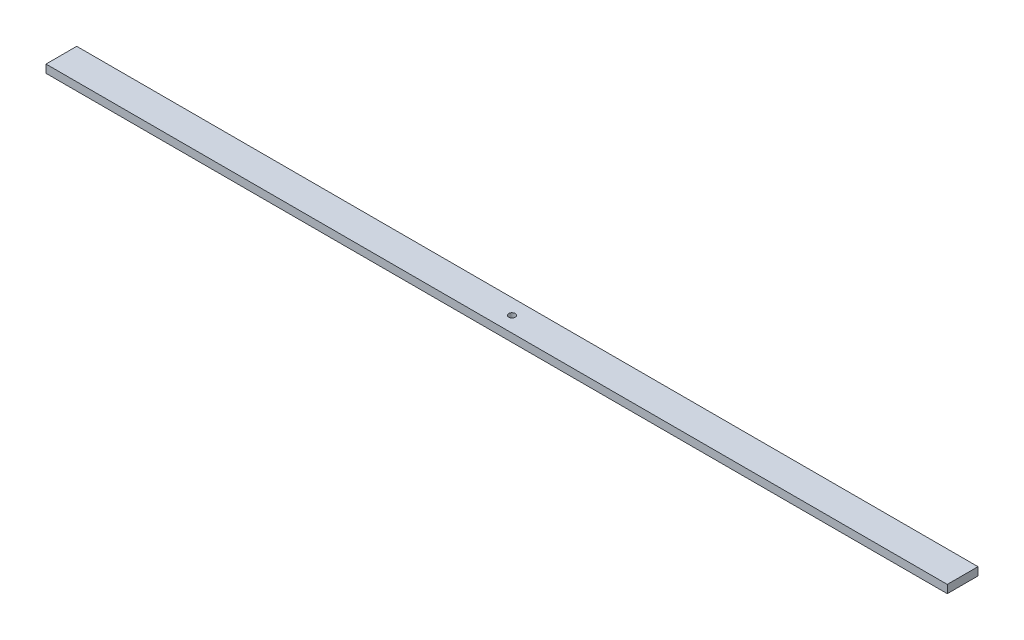
SolidWorks part; units mm, degrees
material "Thornel Mat VMA"
ref_plane "Front Plane" through (0, 0, 0) normal (0, 0, 1) x (1, 0, 0)
ref_plane "Top Plane" through (0, 0, 0) normal (0, 1, 0) x (1, 0, 0)
ref_plane "Right Plane" through (0, 0, 0) normal (1, 0, 0) x (0, 0, -1)
sketch "Sketch1" plane through (0, 0, 0) normal (0, 1, 0) x (1, 0, 0)
  line L1 (-279.4, 9.525) -> (279.4, 9.525)
  line L2 (-279.4, 9.525) -> (-279.4, -9.525)
  line L3 (-279.4, -9.525) -> (279.4, -9.525)
  line L4 (279.4, 9.525) -> (279.4, -9.525)
  line L5 (-279.4, 9.525) -> (279.4, -9.525) construction
  line L6 (-279.4, -9.525) -> (279.4, 9.525) construction
  circle A0 centre (0, 0) radius 2
  point P0 (0, 0)
  dimension "D3" = 4
  dimension "D1" = 19.05
  dimension "D2" = 558.8
extrude "Boss-Extrude1" add sketch "Sketch1" along normal blind 5
